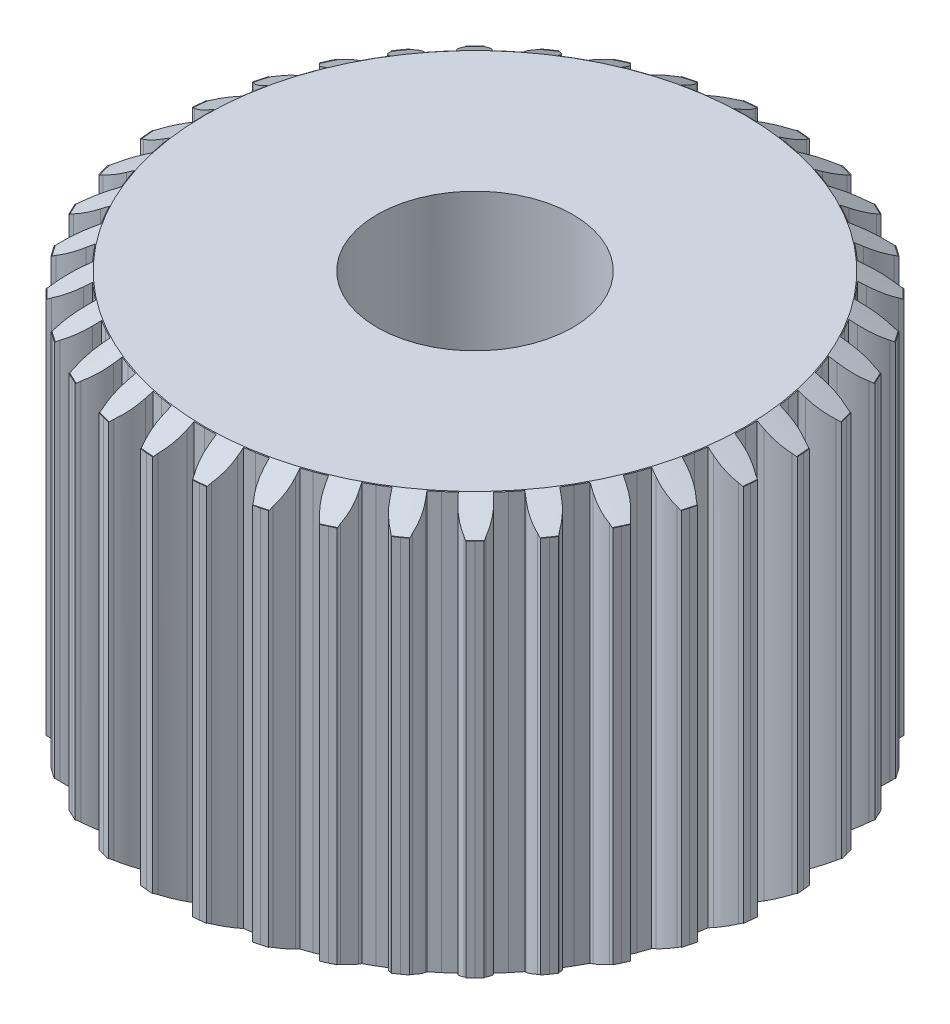
SolidWorks part; units mm, degrees
material "ABS"
ref_plane "Front Plane" through (0, 0, 0) normal (0, 0, 1) x (1, 0, 0)
ref_plane "Top Plane" through (0, 0, 0) normal (0, 1, 0) x (1, 0, 0)
ref_plane "Right Plane" through (0, 0, 0) normal (1, 0, 0) x (0, 0, -1)
sketch "Sketch1" plane through (0, 0, 0) normal (0, 1, 0) x (1, 0, 0)
  line L0 (0, 0) -> (2.325, 0) construction
  line L1 (0, 0) -> (2.3162, 0.2026) construction
  line L2 (0, 0) -> (2.073, 0.0905) construction
  line L3 (2.075, 0) -> (0, 0)
  line L4 (0, 0) -> (2.0435, 0.3603)
  line L5 (2.073, 0.0905) -> (2.075, 0)
  line L6 (2.0558, 0.2815) -> (2.0435, 0.3603)
  line L7 (2.073, 0.0905) -> (2.123, 0.0927)
  line L8 (2.2918, 0.14) -> (2.32, 0.1528)
  line L9 (2.0558, 0.2815) -> (2.1056, 0.2858)
  line L10 (2.2813, 0.2601) -> (2.3113, 0.2524)
  line L11 (2.3113, 0.2524) -> (2.3162, 0.2026)
  line L12 (2.3162, 0.2026) -> (2.32, 0.1528)
  circle A0 centre (0, 0) radius 2.325 construction
  circle A1 centre (0, 0) radius 2.075 construction
  arc A4 (2.123, 0.0927) -> (2.2918, 0.14) centre (2.1062, 0.4772) ccw
  arc A5 (2.1056, 0.2858) -> (2.2813, 0.2601) centre (2.1392, -0.0976) cw
  dimension "D1" = 4.65
  dimension "D2" = 4.15
  dimension "D3" = 5
  dimension "D4" = 2.5
  dimension "D5" = 0.05
  dimension "D6" = 0.05
  dimension "D7" = 0.03
  dimension "D8" = 0.05
  dimension "D9" = 110
  dimension "D10" = 110
extrude "Boss-Extrude1" add sketch "Sketch1" along normal blind 3.2
pattern_circular "CirPattern1" count 36 over 360 about axis through (0, 0, 0) along (0, 1, 0) of "Boss-Extrude1"
sketch "Sketch2" plane through (0, 0, 0) normal (0, -1, 0) x (1, 0, 0)
  circle A0 centre (0, 0) radius 0.75
  dimension "D1" = 1.5
extrude "Cut-Extrude1" cut sketch "Sketch2" against normal blind 1
sketch "Sketch3" plane through (0, 0, 0) normal (0, 0, 1) x (1, 0, 0)
  line L0 (-2.37, 0.15) -> (-2.32, 0.15)
  line L1 (-2.32, 3.05) -> (-2.07, 3.2)
  line L2 (-2.024, 3.2) -> (-2.2014, 3.2) construction
  line L3 (-2.37, 3.2) -> (-2.07, 3.2)
  line L4 (-2.07, 0) -> (-2.37, 0)
  line L5 (-2.2014, 0) -> (-2.024, 0) construction
  line L6 (-2.07, 0) -> (-2.32, 0.15)
  line L7 (-2.32, 3.2) -> (-2.32, 0) construction
  line L9 (-2.37, 0.15) -> (-2.37, 0)
  line L10 (-2.37, 3.2) -> (-2.37, 3.05)
  line L11 (-2.37, 3.05) -> (-2.32, 3.05)
  dimension "D1" = 0.3
  dimension "D2" = 0.15
  dimension "D3" = 0.3
  dimension "D4" = 0.15
ref_axis "Axis1" through (0, 0, 0) along (0, 1, 0)
revolve "Cut-Revolve1" cut sketch "Sketch3" angle 360 about axis through (0, 0, 0) along (0, 1, 0)
sketch "Sketch4" plane through (0, 3.2, 0) normal (0, 1, 0) x (1, 0, 0)
  circle A0 centre (0, 0) radius 0.75
  dimension "D1" = 1.5
extrude "Cut-Extrude2" cut sketch "Sketch4" against normal up to surface (3.2 mm away) up to face at (0, 0, -0.75)
